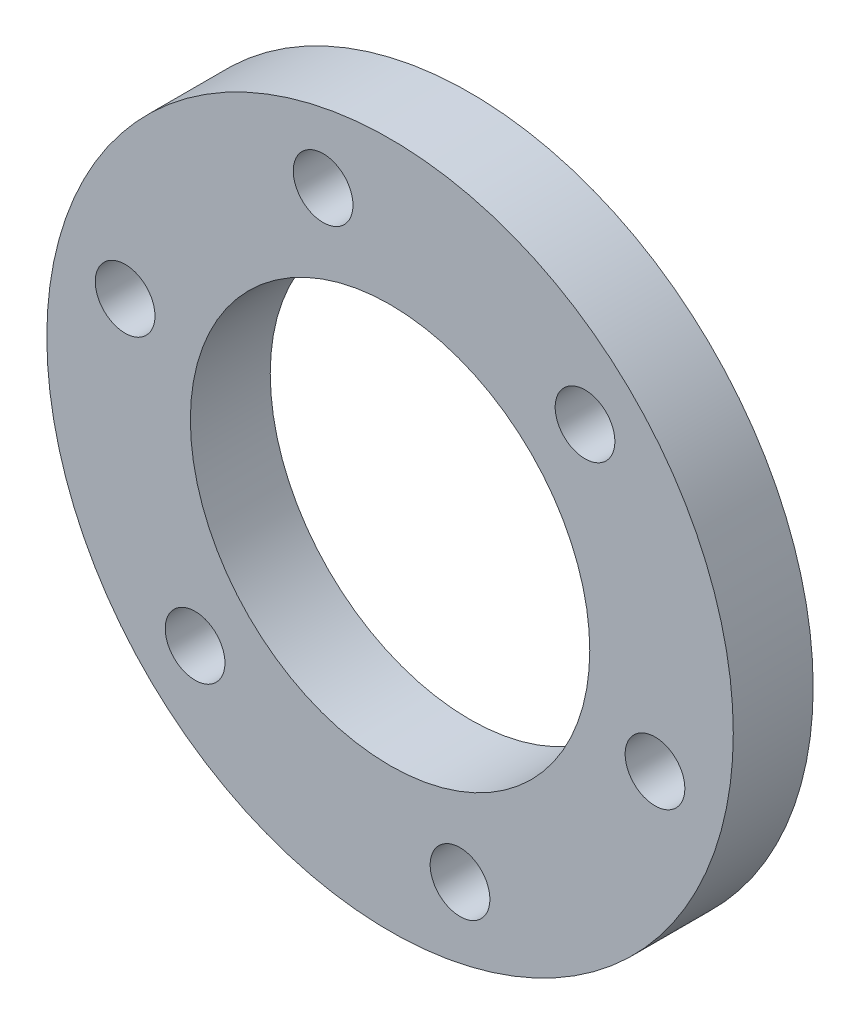
SolidWorks part; units mm, degrees
ref_plane "Front Plane" through (0, 0, 0) normal (0, 0, 1) x (1, 0, 0)
ref_plane "Top Plane" through (0, 0, 0) normal (0, 1, 0) x (1, 0, 0)
ref_plane "Right Plane" through (0, 0, 0) normal (1, 0, 0) x (0, 0, -1)
sketch "Sketch1" plane through (0, 0, 0) normal (0, 0, 1) x (1, 0, 0)
  circle A0 centre (0, 0) radius 21.8281
  circle A1 centre (0, 0) radius 12.7
  dimension "D1" = 25.4
  dimension "D2" = 43.6562
extrude "Boss-Extrude1" add sketch "Sketch1" along normal blind 5.08
hole_wizard "#6 Clearance Hole1" positions "Sketch2" profile "Sketch3" hole size "#6" standard "ANSI Inch" end condition through all
sketch "Sketch2" plane through (0, 0, 5.08) normal (0, 0, 1) x (1, 0, 0)
  point P0 (-4.2574, 16.9819)
  point P2 (12.3987, 12.2968)
  point P5 (16.8487, -4.5892)
  point P8 (4.45, -16.886)
  point P11 (-12.3987, -12.2968)
  point P14 (-16.8487, 4.5892)
sketch "Sketch3" plane through (-4.2574, 16.9819, 5.08) normal (1, 0, 0) x (0, -1, 0)
  line L0 (0, 0) -> (0, 5.08)
  line L1 (0, 5.08) -> (1.8986, 5.08)
  line L2 (1.8986, 5.08) -> (1.8986, 0)
  line L5 (1.8986, 0) -> (0, 0)
  line L11 (0, -6.35) -> (0, 107.95) construction
  dimension "Thru Hole Dia." = 3.7973
  dimension "Thru Hole Depth" = 5.08
